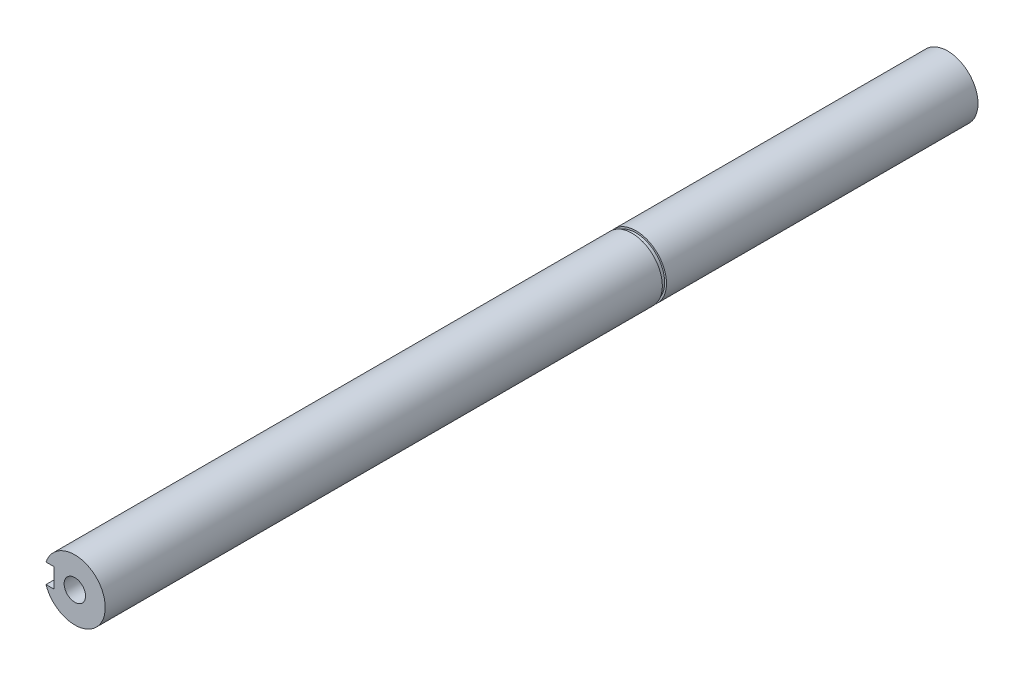
SolidWorks part; units mm, degrees
material "AISI 1020"
ref_plane "Спереди" through (0, 0, 0) normal (0, 0, 1) x (1, 0, 0)
ref_plane "Сверху" through (0, 0, 0) normal (0, 1, 0) x (1, 0, 0)
ref_plane "Справа" through (0, 0, 0) normal (1, 0, 0) x (0, 0, -1)
sketch "Эскиз1" plane through (0, 0, 0) normal (0, 0, 1) x (1, 0, 0)
  circle A0 centre (0, -291.8076) radius 12.5 construction
  circle A1 centre (0, -291.8076) radius 12.5
extrude "Бобышка-Вытянуть1" add sketch "Эскиз1" against normal offset from surface (358.6 mm away) 2 contours A1
sketch "Эскиз2" plane through (0, 0, 0) normal (0, 0, 1) x (1, 0, 0)
  line L0 (-8.3075, -159.8076) -> (-8.3075, -151.8076) construction
  line L1 (-16.5, -287.8076) -> (-8.5, -287.8076)
  line L2 (-16.5, -287.8076) -> (-16.5, -295.8076)
  line L3 (-16.5, -295.8076) -> (-8.5, -295.8076)
  line L4 (-8.5, -287.8076) -> (-8.5, -295.8076)
  line L5 (-16.5, -287.8076) -> (-8.5, -295.8076) construction
  line L6 (-16.5, -295.8076) -> (-8.5, -287.8076) construction
  circle A0 centre (0, -291.8076) radius 12.5 construction
  point P0 (-12.5, -291.8076)
  point P14 (0, -291.8076)
extrude "Вырез-Вытянуть1" cut sketch "Эскиз2" against normal up to surface (30 mm away)
sketch "Эскиз3" plane through (0, 0, -230.6) normal (0, 0, -1) x (-1, 0, 0)
  circle A0 centre (0, -291.8076) radius 11.75
  arc A1 (-11.5219, -294.1115) -> (-11.5219, -289.5037) centre (0, -291.8076) ccw construction
  circle A2 centre (0, -291.8076) radius 26
  circle A3 centre (0, -291.8076) radius 26 construction
extrude "Вырез-Вытянуть2" cut sketch "Эскиз3" against normal blind 1.7
sketch "Эскиз4" plane through (0, 0, -358.6) normal (0, 0, -1) x (-1, 0, 0)
  line L1 (16.5, -295.8076) -> (8.5, -295.8076)
  line L2 (16.5, -295.8076) -> (16.5, -287.8076)
  line L3 (16.5, -287.8076) -> (8.5, -287.8076)
  line L4 (8.5, -295.8076) -> (8.5, -287.8076)
  line L5 (16.5, -295.8076) -> (8.5, -287.8076) construction
  line L6 (16.5, -287.8076) -> (8.5, -295.8076) construction
  circle A0 centre (0, -291.8076) radius 12.5 construction
  point P0 (12.5, -291.8076)
  point P7 (0, -291.8076)
  point P8 (0, -291.8076)
  dimension "D1" = 8
extrude "Вырез-Вытянуть3" cut sketch "Эскиз4" against normal up to surface (128 mm away)
hole_wizard "Сверление под метчик M10x1.252" positions "Эскиз5" profile "Эскиз6" hole size "M10x1.25" standard "Ansi Metric"
sketch "Эскиз5" plane through (0, 0, 0) normal (0, 0, 1) x (1, 0, 0)
  point P0 (0, -291.8076)
sketch "Эскиз6" plane through (0, -291.8076, 0) normal (1, 0, 0) x (0, -1, 0)
  line L0 (0, 0) -> (0, 35.1438)
  line L1 (0, 35.1438) -> (4.4, 32.5)
  line L2 (4.4, 32.5) -> (4.4, 0)
  line L5 (4.4, 0) -> (0, 0)
  line L10 (0, 35.1438) -> (-4.4, 32.5) construction
  line L11 (0, -6.35) -> (0, 107.95) construction
  dimension "Диаметр отверстия" = 8.8
  dimension "Глубина отверстия" = 32.5
  dimension "Угол заточки сверла" = 118
cosmetic thread "Условное изображение резьбы1" parameters "D2"=10
hole_wizard "Сверление под метчик M10x1.253" positions "Эскиз10" profile "Эскиз11" hole size "M10x1.25" standard "Ansi Metric"
sketch "Эскиз10" plane through (0, 0, -358.6) normal (0, 0, -1) x (-1, 0, 0)
  point P0 (0, -291.8076)
sketch "Эскиз11" plane through (0, -291.8076, -358.6) normal (1, 0, 0) x (0, 1, 0)
  line L0 (0, 0) -> (0, 35.1438)
  line L1 (0, 35.1438) -> (4.4, 32.5)
  line L2 (4.4, 32.5) -> (4.4, 0)
  line L5 (4.4, 0) -> (0, 0)
  line L10 (0, 35.1438) -> (-4.4, 32.5) construction
  line L11 (0, -6.35) -> (0, 107.95) construction
  dimension "Диаметр отверстия" = 8.8
  dimension "Глубина отверстия" = 32.5
  dimension "Угол заточки сверла" = 118
cosmetic thread "Условное изображение резьбы2" parameters "D2"=10
